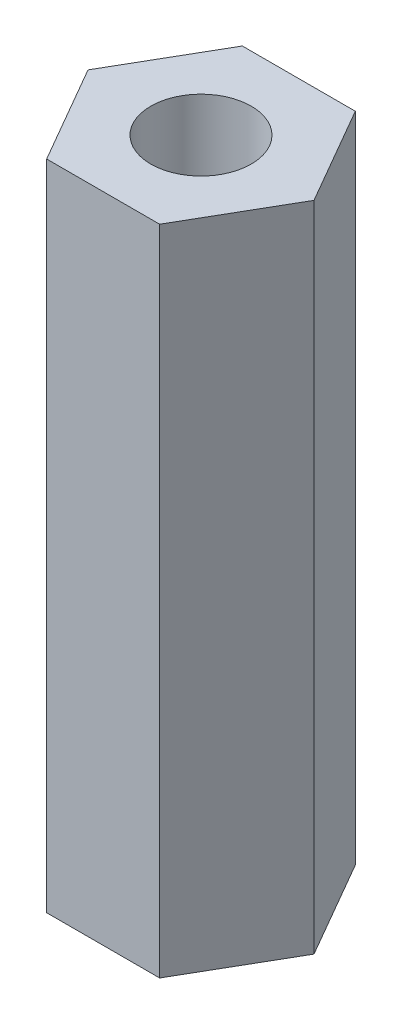
SolidWorks part; units mm, degrees
ref_plane "Front Plane" through (0, 0, 0) normal (0, 0, 1) x (1, 0, 0)
ref_plane "Top Plane" through (0, 0, 0) normal (0, 1, 0) x (1, 0, 0)
ref_plane "Right Plane" through (0, 0, 0) normal (1, 0, 0) x (0, 0, -1)
sketch "Sketch1" plane through (0, 0, 0) normal (0, 1, 0) x (1, 0, 0)
  line L1 (2.25, 0) -> (1.125, 1.9486)
  line L2 (1.125, 1.9486) -> (-1.125, 1.9486)
  line L3 (-1.125, 1.9486) -> (-2.25, 0)
  line L4 (-2.25, 0) -> (-1.125, -1.9486)
  line L5 (-1.125, -1.9486) -> (1.125, -1.9486)
  line L6 (1.125, -1.9486) -> (2.25, 0)
  circle A0 centre (0, 0) radius 1.9486 construction
  circle A1 centre (0, 0) radius 1
  dimension "D2" = 2
  dimension "D1" = 4.5
extrude "Boss-Extrude1" add sketch "Sketch1" along normal blind 13
